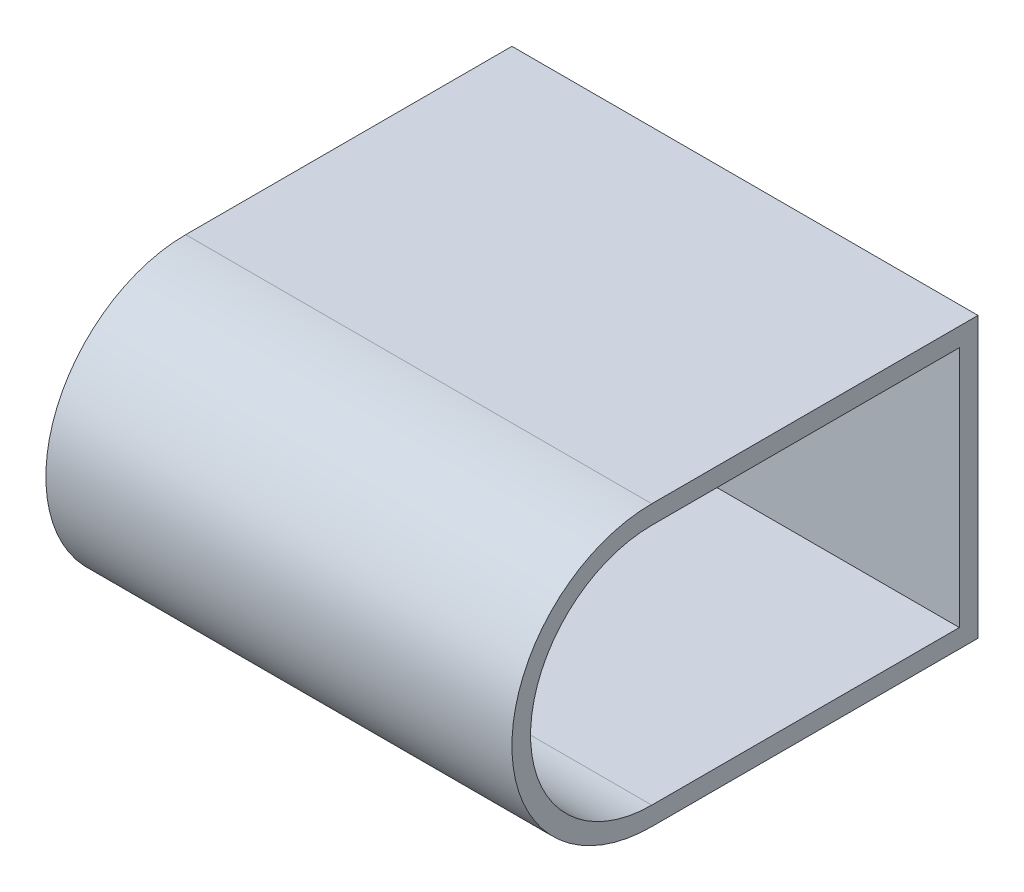
SolidWorks part; units mm, degrees
ref_plane "Plan de face" through (0, 0, 0) normal (0, 0, 1) x (1, 0, 0)
ref_plane "Plan de dessus" through (0, 0, 0) normal (0, 1, 0) x (1, 0, 0)
ref_plane "Plan de droite" through (0, 0, 0) normal (1, 0, 0) x (0, 0, -1)
sketch "Esquisse1" plane through (0, 0, 0) normal (0, 0, 1) x (1, 0, 0)
  line L0 (0, 0) -> (50, 0)
  dimension "D1" = 50
other "Tube biseauté TUBE BISEAUTÉ 1(1)"
ref_plane "Plan1" through (0, 0, 0) normal (1, 0, 0) x (0, 1, 0)
sketch "Esquisse11" plane through (0, 0, 0) normal (1, 0, 0) x (0, 1, 0)
  line L0 (-15, 0) -> (-15, 35)
  line L1 (15, 35) -> (15, 0)
  line L2 (15, 0) -> (-15, 0)
  line L3 (-13, 2) -> (-13, 35)
  line L4 (13, 35) -> (13, 2)
  line L5 (13, 2) -> (-13, 2)
  arc A0 (-15, 35) -> (15, 35) centre (0, 35) cw
  arc A1 (-13, 35) -> (13, 35) centre (0, 35) cw
  point P11 (0, 0)
  dimension "D2" = 50
  dimension "D1" = 30
  dimension "D3" = 2
sketch "Esquisse12" plane through (0, 0, 0) normal (-1, 0, 0) x (0, 0, 1)
  line L0 (35, -13) -> (2, -13) construction
  line L1 (2, 13) -> (35, 13) construction
  line L2 (2, -13) -> (2, 13) construction
  line L3 (35, -13) -> (2, -13)
  line L4 (2, 13) -> (35, 13)
  line L5 (2, -13) -> (2, 13)
  arc A0 (35, -13) -> (35, 13) centre (35, 0) ccw construction
  arc A1 (35, -13) -> (35, 13) centre (35, 0) ccw
  circle A2 centre (35, 0) radius 5
  dimension "D1" = 10
extrude "Boss.-Extru.1" add sketch "Esquisse12" against normal blind 2 separate body
